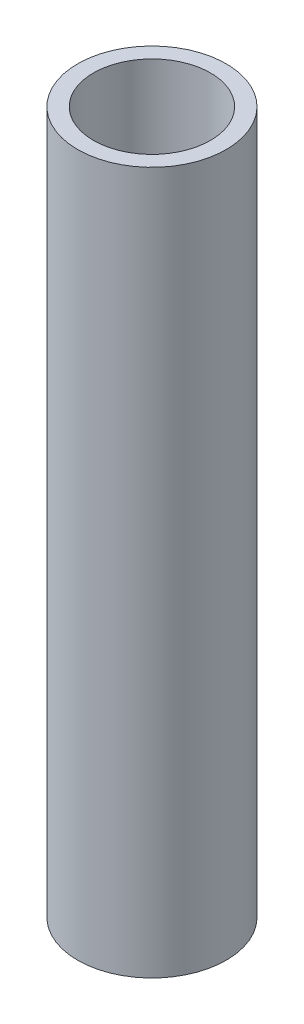
SolidWorks part; units mm, degrees
ref_plane "Plan de face" through (0, 0, 0) normal (0, 0, 1) x (1, 0, 0)
ref_plane "Plan de dessus" through (0, 0, 0) normal (0, 1, 0) x (1, 0, 0)
ref_plane "Plan de droite" through (0, 0, 0) normal (1, 0, 0) x (0, 0, -1)
sketch "Esquisse1" plane through (0, 0, 0) normal (0, 1, 0) x (1, 0, 0)
  circle A0 centre (0, 0) radius 3.175
  circle A1 centre (0, 0) radius 2.5
  dimension "D1" = 6.35
  dimension "D2" = 5
extrude "Boss.-Extru.1" add sketch "Esquisse1" along normal blind 30 contours A0 | A1
